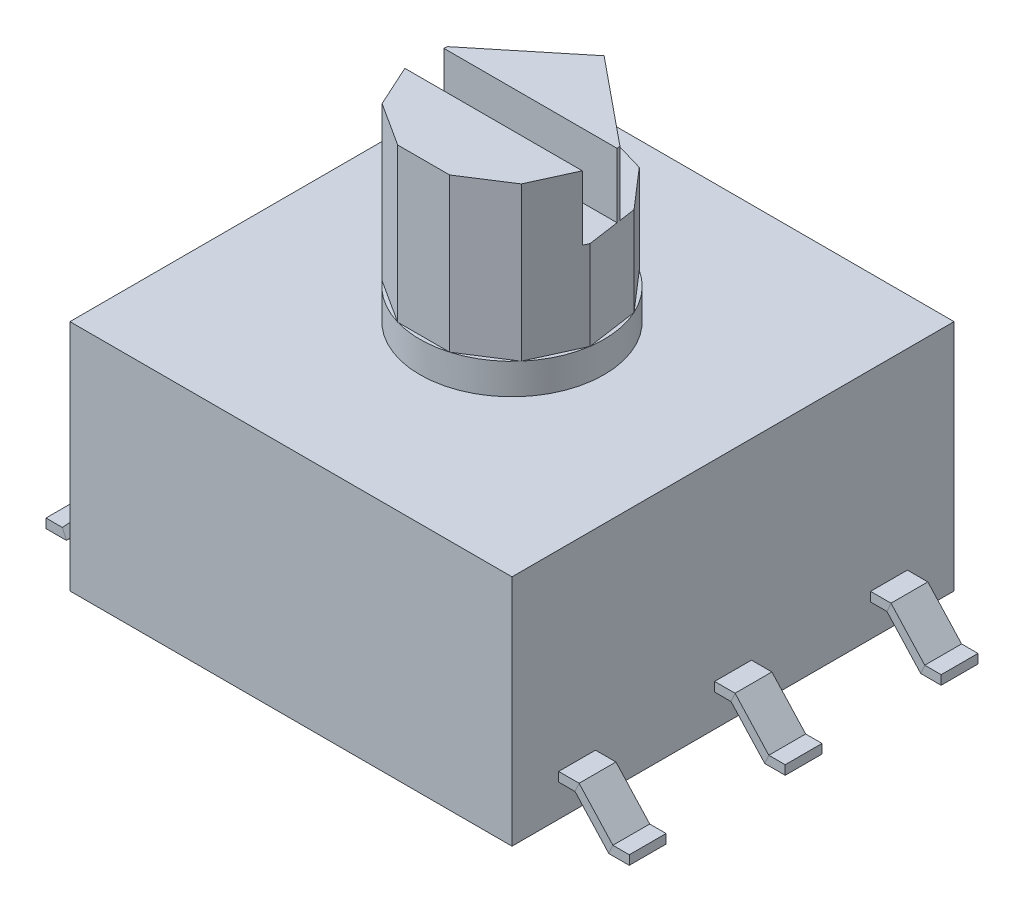
SolidWorks part; units mm, degrees
ref_plane "Front Plane" through (0, 0, 0) normal (0, 0, 1) x (1, 0, 0)
ref_plane "Top Plane" through (0, 0, 0) normal (0, 1, 0) x (1, 0, 0)
ref_plane "Right Plane" through (0, 0, 0) normal (1, 0, 0) x (0, 0, -1)
sketch "Sketch1" plane through (0, 0, 0) normal (0, 1, 0) x (1, 0, 0)
  line L0 (3.6, -3.6) -> (-3.6, 3.6) construction
  line L1 (-3.6, -3.6) -> (3.6, -3.6)
  line L2 (-3.6, -3.6) -> (-3.6, 3.6)
  line L3 (-3.6, 3.6) -> (3.6, 3.6)
  line L4 (3.6, -3.6) -> (3.6, 3.6)
  dimension "D1" = 7.2
extrude "Boss-Extrude1" add sketch "Sketch1" along normal blind 3.8 contours L3 L4 L1 L2
sketch "Sketch2" plane through (0, 3.8, 0) normal (0, 1, 0) x (1, 0, 0)
  circle A0 centre (0, 0) radius 1.5
  dimension "D1" = 3
extrude "Boss-Extrude2" add sketch "Sketch2" along normal blind 3
sketch "Sketch3" plane through (0, 6.8, 0) normal (0, 1, 0) x (1, 0, 0)
  line L0 (0, 0) -> (0, 1.5) construction
  line L1 (0, 1.5) -> (-0.811, 1.2619)
  line L2 (-0.811, 1.2619) -> (-1.3644, 0.6231)
  line L3 (-1.3644, 0.6231) -> (-1.4847, -0.2135)
  line L4 (-1.4847, -0.2135) -> (-1.1336, -0.9823)
  line L5 (-1.1336, -0.9823) -> (-0.4226, -1.4392)
  line L6 (-0.4226, -1.4392) -> (0.4226, -1.4392)
  line L7 (0.4226, -1.4392) -> (1.1336, -0.9823)
  line L8 (1.1336, -0.9823) -> (1.4847, -0.2135)
  line L9 (1.4847, -0.2135) -> (1.3644, 0.6231)
  line L10 (1.3644, 0.6231) -> (0.811, 1.2619)
  line L11 (0.811, 1.2619) -> (0, 1.5)
  circle A0 centre (0, 0) radius 1.4392 construction
  circle A1 centre (0, 0) radius 1.65
  circle A2 centre (0, 0) radius 1.5 construction
  dimension "D1" = 3.3
extrude "Cut-Extrude1" cut sketch "Sketch3" against normal blind 2.5
sketch "Sketch4" plane through (0, 6.8, 0) normal (0, 1, 0) x (1, 0, 0)
  line L0 (-2.3098, 0.3) -> (1.4697, 0.3)
  line L2 (1.4697, -0.3) -> (-1.4697, -0.3)
  line L4 (-1.4697, -0.3) -> (1.4697, 0.3) construction
  line L5 (-1.4697, 0.3) -> (1.4697, 0.3)
  line L6 (1.4697, 0.3) -> (0, 1.5)
  line L7 (0, 1.5) -> (-1.4697, 0.3)
  line L8 (0, 1.5) -> (0, 0.3) construction
  line L9 (0, 0) -> (0, 0.3) construction
  circle A0 centre (0, 0) radius 1.5
  arc A3 (-1.3644, 0.6231) -> (-1.4847, -0.2135) centre (0, 0) ccw construction
  line M9 (1.3644, 0.6231) -> (0.811, 1.2619)
  line M10 (0.811, 1.2619) -> (0, 1.5)
  line M11 (0, 1.5) -> (-0.811, 1.2619)
  line M12 (-0.811, 1.2619) -> (-1.3644, 0.6231)
  line M13 (-1.3644, 0.6231) -> (-1.4847, -0.2135)
  line M14 (-1.4847, -0.2135) -> (-1.1336, -0.9823)
  line M18 (1.1336, -0.9823) -> (1.4847, -0.2135)
  line M19 (1.4847, -0.2135) -> (1.3644, 0.6231)
  dimension "D1" = 0.6
extrude "Cut-Extrude2" cut sketch "Sketch4" against normal blind 1.05 contours L2 L0 M18 M19 M13 M14 | L7 M11 M12 M13 | L6 M19 M9 M10
sketch "Sketch5" plane through (0, 0, 0) normal (0, 0, 1) x (1, 0, 0)
  line L0 (3.6, 0.6) -> (3.9, 0.6)
  line L1 (3.6, 3.8) -> (3.6, 0) construction
  line L2 (3.9, 0.6) -> (4.45, 0)
  line L3 (4.45, 0) -> (4.75, 0)
  line L4 (0, 0) -> (0, -0.7776) construction
  line L8 (-3.6, 0) -> (3.6, 0) construction
  dimension "D1" = 4.75
  dimension "D2" = 0.3
  dimension "D3" = 0.6
sketch "Sketch6" plane through (3.6, 0, 0) normal (1, 0, 0) x (0, 0, -1)
  line L0 (0.3, 0.525) -> (-0.3, 0.675) construction
  line L1 (-0.3, 0.675) -> (0.3, 0.675)
  line L2 (-0.3, 0.675) -> (-0.3, 0.525)
  line L3 (-0.3, 0.525) -> (0.3, 0.525)
  line L4 (0.3, 0.675) -> (0.3, 0.525)
  line L5 (0, 0.6) -> (0, 0) construction
  point P4 (0, 0.6)
  dimension "D1" = 0.15
  dimension "D2" = 0.6
sweep "Sweep1" add profiles "Sketch6" path "Sketch5"
pattern_linear "LPattern1" count 2 spacing 2.54 along (0, 0, -1) count 2 spacing 2.54 along (0, 0, 1) of "Sweep1"
mirror "Mirror1" about plane through (0, 0, 0) normal (1, 0, 0) of "LPattern1", "Sweep1"
